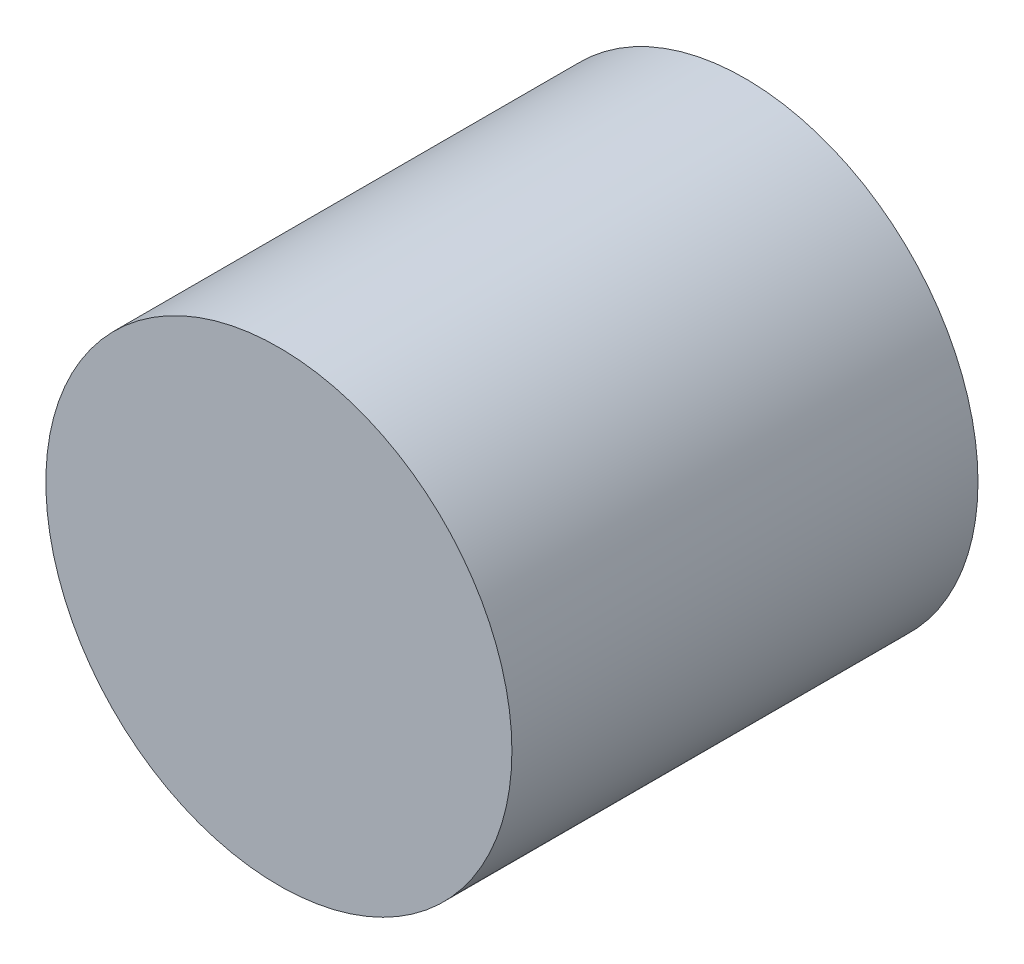
SolidWorks part; units mm, degrees
ref_plane "Front" through (0, 0, 0) normal (0, 0, 1) x (1, 0, 0)
ref_plane "Top" through (0, 0, 0) normal (0, 1, 0) x (1, 0, 0)
ref_plane "Right" through (0, 0, 0) normal (1, 0, 0) x (0, 0, -1)
sketch "Sketch1" plane through (0, 0, 0) normal (0, 0, 1) x (1, 0, 0)
  circle A0 centre (0, 0) radius 2
  dimension "D1" = 4
extrude "Boss-Extrude1" add sketch "Sketch1" along normal blind 4
